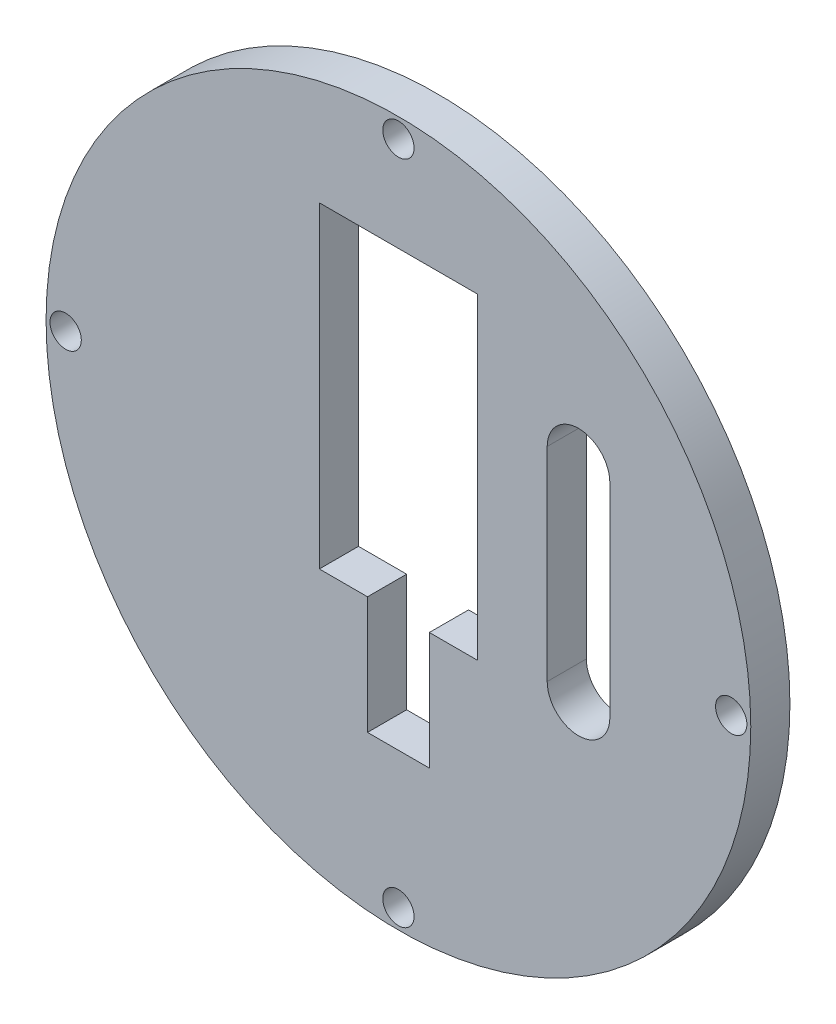
SolidWorks part; units mm, degrees
ref_plane "Front Plane" through (0, 0, 0) normal (0, 0, 1) x (1, 0, 0)
ref_plane "Top Plane" through (0, 0, 0) normal (0, 1, 0) x (1, 0, 0)
ref_plane "Right Plane" through (0, 0, 0) normal (1, 0, 0) x (0, 0, -1)
sketch "Sketch1" plane through (0, 0, 0) normal (0, 0, 1) x (1, 0, 0)
  line L0 (0, 61.1562) -> (0, -62.0155) construction
  line L1 (-10.1, 30.4) -> (10.1, 30.4)
  line L2 (-10.1, 30.4) -> (-10.1, -10.1)
  line L3 (-10.1, -10.1) -> (10.1, -10.1)
  line L4 (10.1, 30.4) -> (10.1, -10.1)
  line L5 (-10.1, 30.4) -> (10.1, -10.1) construction
  line L6 (-10.1, -10.1) -> (10.1, 30.4) construction
  line L7 (-62.9195, 0) -> (73.7046, 0) construction
  circle A0 centre (0, 0) radius 45
  circle A1 centre (0, 0) radius 1.25 construction
  circle A6 centre (42.5, 0) radius 2
  circle A7 centre (0, -42.5) radius 2
  circle A8 centre (-42.5, 0) radius 2
  circle A9 centre (0, 42.5) radius 2
  circle A10 centre (0, 0) radius 42.5 construction
  point P2 (0, 10.15)
  point P11 (5, -92.894)
  point P12 (5, 90.4881)
  point P13 (-96.2355, -5)
  point P14 (94.097, -5)
  point P15 (-5, -92.894)
  point P16 (-5, 90.4881)
  point P17 (-96.2355, 5)
  point P18 (94.097, 5)
  point P35 (0, 0)
  dimension "D1" = 90
  dimension "D5" = 2.5
  dimension "D14" = 4
  dimension "D13" = 85
  dimension "D2" = 20.2
  dimension "D3" = 40.5
  dimension "D15" = 4
  dimension "D4" = 10.1
extrude "Boss-Extrude1" add sketch "Sketch1" along normal blind 5
sketch "Sketch2" plane through (0, 0, 0) normal (0, 0, -1) x (-1, 0, 0)
  line L0 (10.1, -10.1) -> (-10.1, -10.1) construction
  line L1 (-3.95, -10.1) -> (3.95, -10.1)
  line L2 (-3.95, -10.1) -> (-3.95, -25.1)
  line L3 (-3.95, -25.1) -> (3.95, -25.1)
  line L4 (3.95, -10.1) -> (3.95, -25.1)
  point P4 (0, -10.1)
  dimension "D1" = 7.9
  dimension "D2" = 15
extrude "Cut-Extrude1" cut sketch "Sketch2" against normal blind 10
sketch "Sketch3" plane through (0, 0, 0) normal (0, 0, -1) x (-1, 0, 0)
  line L0 (-23, 18) -> (-23, -8) construction
  line L1 (-19, 18) -> (-19, -8)
  line L2 (-27, 18) -> (-27, -8)
  arc A0 (-19, 18) -> (-27, 18) centre (-23, 18) ccw
  arc A1 (-27, -8) -> (-19, -8) centre (-23, -8) ccw
  point P2 (-23, 5)
  dimension "D1" = 4
  dimension "D2" = 23
  dimension "D3" = 5
  dimension "D4" = 18
extrude "Cut-Extrude2" cut sketch "Sketch3" against normal blind 10
